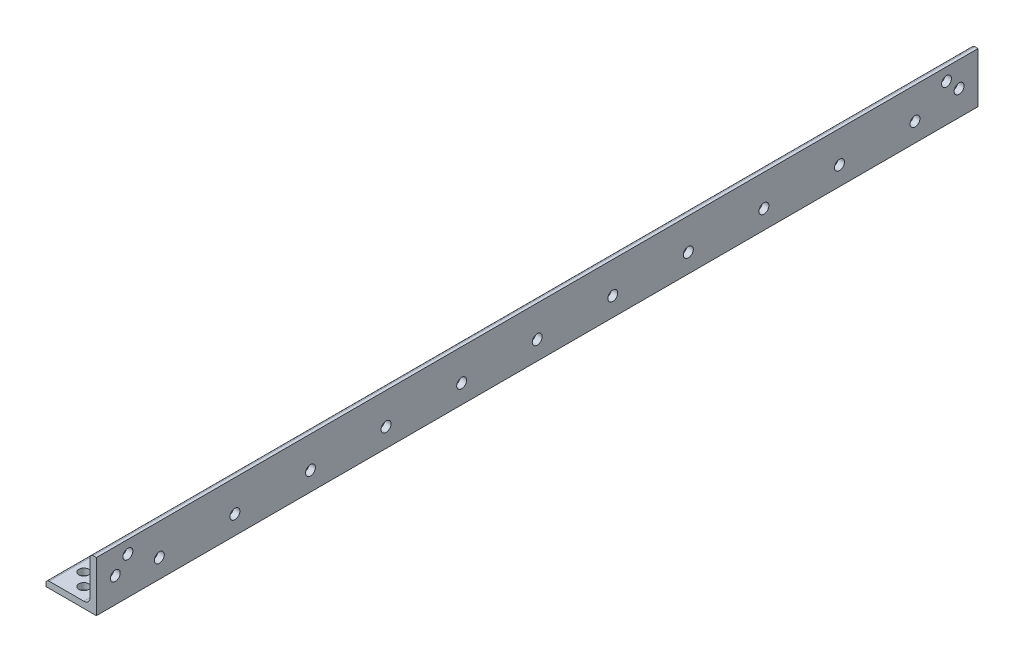
SolidWorks part; units mm, degrees
ref_plane "Front Plane" through (0, 0, 0) normal (0, 0, 1) x (1, 0, 0)
ref_plane "Top Plane" through (0, 0, 0) normal (0, 1, 0) x (1, 0, 0)
ref_plane "Right Plane" through (0, 0, 0) normal (1, 0, 0) x (0, 0, -1)
sketch "Sketch0" plane through (0, 0, 0) normal (0, 0, 1) x (1, 0, 0)
  line L0 (-12.7, -12.7) -> (12.7, -12.7)
  line L1 (12.7, -12.7) -> (12.7, 12.7)
  line L2 (12.7, 0) -> (0, 0) construction
  line L3 (0, 0) -> (0, -12.7) construction
  line L4 (9.525, -6.35) -> (9.525, 12.7) construction
  line L5 (6.35, -9.525) -> (-12.7, -9.525) construction
  arc A0 (9.525, -6.35) -> (6.35, -9.525) centre (6.35, -6.35) cw
  point P3 (8.5951, -8.5951)
  dimension "Inside Corner Radius" = 3.175
  dimension "Outside Height" = 25.4
  dimension "Inside Height" = 22.225
  dimension "Inside Width" = 22.225
  dimension "Wall Thickness" = 3.175
  dimension "D1" = 3.175
  dimension "Outside Width" = 25.4
sketch "Sketch1" plane through (0, 0, 0) normal (1, 0, 0) x (0, 0, -1)
  line L0 (304.8, 0) -> (-304.8, 0)
  point P4 (0, 0)
  dimension "Length" = 609.6
sketch "Sketch2" plane through (0, 0, 0) normal (0, 0, 1) x (1, 0, 0)
  line L0 (-12.7, -12.7) -> (12.7, -12.7)
  line L1 (12.7, -12.7) -> (12.7, 12.7)
  line L2 (12.7, 12.7) -> (9.525, 12.7) construction
  line L3 (9.525, 11.1125) -> (9.525, -6.35)
  line L4 (6.35, -9.525) -> (-11.1125, -9.525)
  line L5 (-12.7, -12.7) -> (-12.7, -9.525) construction
  line L6 (11.1125, 12.7) -> (12.7, 12.7)
  line L7 (-12.7, -11.1125) -> (-12.7, -12.7)
  line L8 (12.7, 0) -> (0, 0) construction
  line L9 (0, 0) -> (0, -12.7) construction
  arc A0 (9.525, 11.1125) -> (11.1125, 12.7) centre (11.1125, 11.1125) cw
  arc A1 (-12.7, -11.1125) -> (-11.1125, -9.525) centre (-11.1125, -11.1125) cw
  arc A2 (9.525, -6.35) -> (6.35, -9.525) centre (6.35, -6.35) cw
  dimension "Inside Radius" = 3.175
  dimension "Height" = 25.4
  dimension "Width" = 25.4
  dimension "Thickness" = 3.175
extrude "Boss-Extrude1" add sketch "Sketch2" along normal mid plane 609.6
sketch "Break Locations" plane through (0, 0, 0) normal (1, 0, 0) x (0, 0, -1)
  line L0 (-278.892, 0) -> (278.892, 0)
  line L1 (-304.8, -12.7) -> (-304.8, 12.7) construction
  line L2 (304.8, -12.7) -> (304.8, 12.7) construction
  point P0 (-283.21, 0)
  point P1 (283.21, 0)
  point P10 (0, 0)
  point P11 (278.892, 0)
  point P13 (-278.892, 0)
  dimension "D1" = 21.59
  dimension "D2" = 21.59
  dimension "D3" = 25.908
sketch "Sketch7" plane through (0, -12.7, 0) normal (0, -1, 0) x (1, 0, 0)
  line L0 (-12.7, 139.7) -> (12.7, 139.7)
  line L1 (-12.7, 304.8) -> (12.7, 304.8)
  line L2 (-12.7, 304.8) -> (-12.7, -304.8)
  line L3 (-12.7, -304.8) -> (12.7, -304.8)
  line L4 (12.7, 304.8) -> (12.7, -304.8)
  line M4 (12.7, -304.8) -> (12.7, 304.8)
  line M5 (12.7, 304.8) -> (-12.7, 304.8)
  line M6 (-12.7, 304.8) -> (-12.7, -304.8)
  dimension "D1" = 444.5
extrude "Cut-Extrude1" cut sketch "Sketch7" against normal blind 254 contours L0 M6 M4 M5
sketch "Sketch3" plane through (0, 0, 0) normal (0, 1, 0) x (1, 0, 0)
  line L0 (12.7, -139.7) -> (12.7, 304.8) construction
  line L1 (-12.7, 304.8) -> (12.7, 304.8) construction
  line L2 (12.7, -139.7) -> (12.7, 304.8) construction
  line L3 (6.35, 304.8) -> (-11.1125, 304.8) construction
  line L4 (-11.1125, 82.55) -> (6.35, 82.55) construction
  line L5 (-11.1125, -139.7) -> (-11.1125, 304.8) construction
  line L6 (6.35, -139.7) -> (6.35, 304.8) construction
  line L7 (0, 273.05) -> (0, 234.95) construction
  circle A0 centre (-6.35, 292.1) radius 2.5
  circle A1 centre (0, 298.45) radius 2.5
  circle A2 centre (0, 273.05) radius 2.5
  circle A3 centre (0, 234.95) radius 2.5
  circle A4 centre (0, 196.85) radius 2.5
  circle A5 centre (0, 158.75) radius 2.5
  circle A6 centre (0, 120.65) radius 2.5
  circle A7 centre (0, 82.55) radius 2.5
  circle A8 centre (0, 44.45) radius 2.5
  circle A9 centre (0, 6.35) radius 2.5
  circle A10 centre (0, -31.75) radius 2.5
  circle A11 centre (0, -69.85) radius 2.5
  circle A12 centre (0, -107.95) radius 2.5
  circle A13 centre (0, -133.35) radius 2.5
  circle A14 centre (-6.35, -127) radius 2.5
  dimension "D3" = 5
  dimension "D1" = 12.7
  dimension "D2" = 6.35
  dimension "D4" = 19.05
  dimension "D5" = 12.7
  dimension "D6" = 12.7
  dimension "D7" = 31.75
  dimension "D9" = 38.1
  dimension "D8" = 11
extrude "Cut-Extrude2" cut sketch "Sketch3" against normal blind 254
sketch "Sketch8" plane through (12.7, 0, -12.7) normal (-1, 0, 0) x (0, 0, 1)
  line L0 (152.4, -6.35) -> (-292.1, -6.35) construction
  line L1 (152.4, 11.1125) -> (-292.1, 11.1125) construction
  line L2 (152.4, -12.7) -> (-292.1, -12.7) construction
  line L3 (-292.1, 11.1125) -> (-292.1, -6.35) construction
  line L4 (-69.85, 11.1125) -> (-69.85, -6.35) construction
  line L7 (120.65, -3.175) -> (82.55, -3.175) construction
  circle A0 centre (136.525, 6.35) radius 2.5
  circle A1 centre (142.875, 0) radius 2.5
  circle A2 centre (120.65, -3.175) radius 2.5
  circle A3 centre (82.55, -3.175) radius 2.5
  circle A4 centre (44.45, -3.175) radius 2.5
  circle A5 centre (6.35, -3.175) radius 2.5
  circle A6 centre (-31.75, -3.175) radius 2.5
  circle A7 centre (-69.85, -3.175) radius 2.5
  circle A8 centre (-107.95, -3.175) radius 2.5
  circle A9 centre (-146.05, -3.175) radius 2.5
  circle A10 centre (-184.15, -3.175) radius 2.5
  circle A11 centre (-222.25, -3.175) radius 2.5
  circle A12 centre (-260.35, -3.175) radius 2.5
  circle A13 centre (-282.575, 0) radius 2.5
  circle A14 centre (-276.225, 6.35) radius 2.5
  point P4 (-69.85, -6.35)
  point P7 (0, 0)
  point P10 (-69.85, 11.1125)
  point P13 (-281.9455, 0)
  point P16 (-272.5868, 7.2344)
  point P17 (-69.85, 5.7664)
  dimension "D3" = 5
  dimension "D1" = 9.525
  dimension "D2" = 12.7
  dimension "D4" = 9.525
  dimension "D5" = 19.05
  dimension "D6" = 15.875
  dimension "D9" = 38.1
  dimension "D8" = 11
extrude "Cut-Extrude4" cut sketch "Sketch8" along normal blind 254
equation "\"D1@Break Locations\" = .85 * \"Height@Sketch2\""
equation "\"D2@Break Locations\"=\"D1@Break Locations\""
equation "\"Thickness@Sketch2\" = \"Wall Thickness@Sketch0\""
equation "\"Height@Sketch2\" = \"Outside Height@Sketch0\""
equation "\"Width@Sketch2\" = \"Outside Width@Sketch0\""
equation "\"Inside Radius@Sketch2\" = \"Inside Corner Radius@Sketch0\""
equation "\"Length@Boss-Extrude1\" = \"Length@Sketch1\""
equation "\"D3@Break Locations\"=\"D2@Break Locations\"*1.2"
equation "\"D1@Sketch0\"=\"Wall Thickness@Sketch0\""
